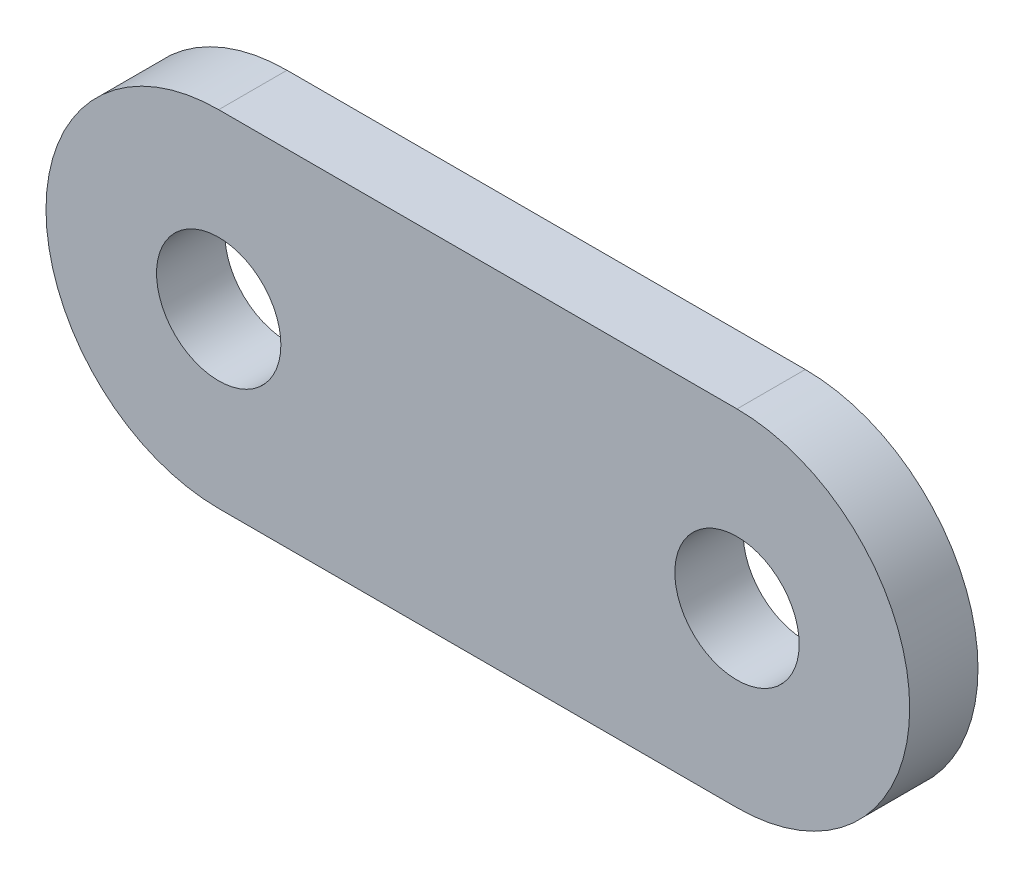
SolidWorks part; units mm, degrees
ref_plane "Front Plane" through (0, 0, 0) normal (0, 0, 1) x (1, 0, 0)
ref_plane "Top Plane" through (0, 0, 0) normal (0, 1, 0) x (1, 0, 0)
ref_plane "Right Plane" through (0, 0, 0) normal (1, 0, 0) x (0, 0, -1)
sketch "Sketch1" plane through (0, 0, 0) normal (0, 0, 1) x (1, 0, 0)
  line L0 (0, 0) -> (33.3502, 0) construction
  line L1 (0, 11.1125) -> (33.3502, 11.1125)
  line L2 (0, -11.1125) -> (33.3502, -11.1125)
  arc A0 (0, 11.1125) -> (0, -11.1125) centre (0, 0) ccw
  arc A1 (33.3502, -11.1125) -> (33.3502, 11.1125) centre (33.3502, 0) ccw
  circle A2 centre (0, 0) radius 4
  circle A3 centre (33.3502, 0) radius 4
  point P3 (16.6751, 0)
  dimension "D2" = 8
  dimension "D1" = 33.3502
  dimension "D3" = 22.225
extrude "Boss-Extrude1" add sketch "Sketch1" along normal blind 4.3942
